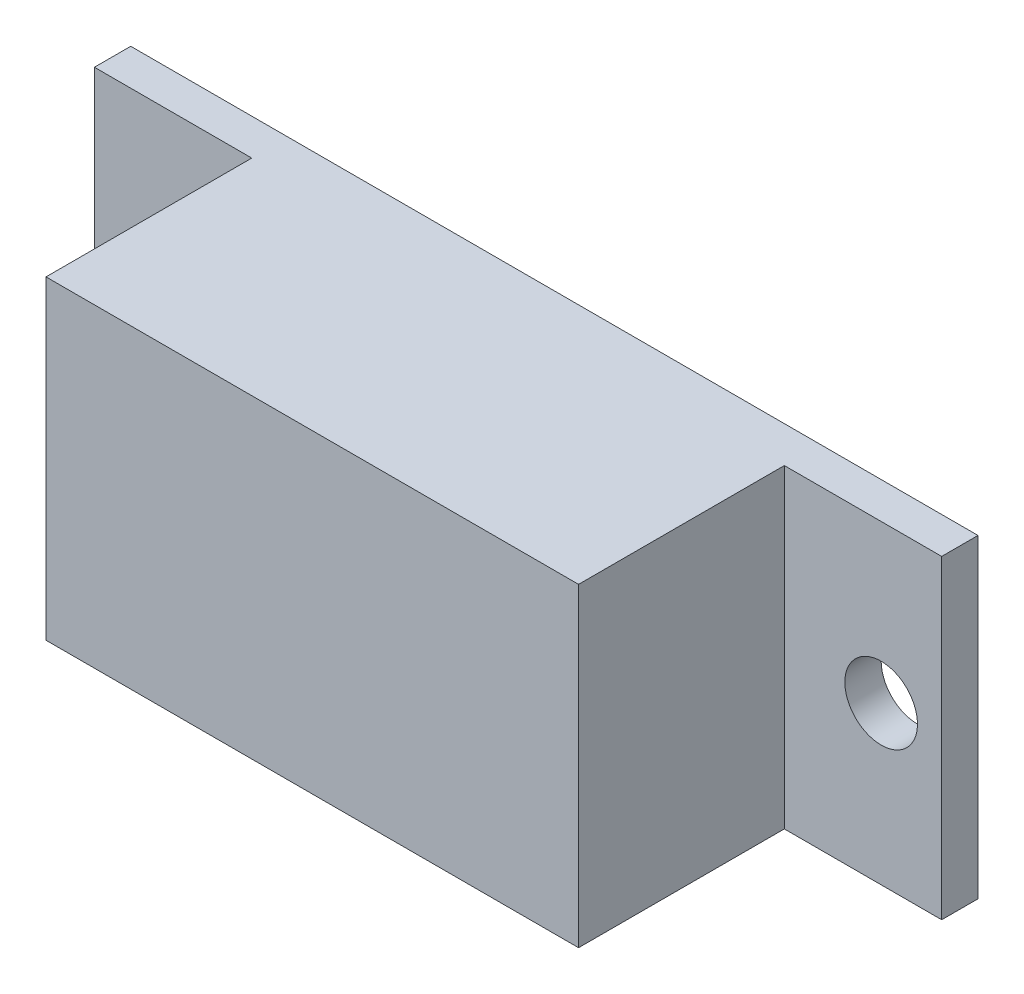
SolidWorks part; units mm, degrees
ref_plane "Plano frontal" through (0, 0, 0) normal (0, 0, 1) x (1, 0, 0)
ref_plane "Plano superior" through (0, 0, 0) normal (0, 1, 0) x (1, 0, 0)
ref_plane "Plano direito" through (0, 0, 0) normal (1, 0, 0) x (0, 0, -1)
sketch "Esboço1" plane through (0, 0, 0) normal (0, 0, 1) x (1, 0, 0)
  line L1 (0, 0) -> (35, 0)
  line L2 (0, 0) -> (0, 13)
  line L3 (0, 13) -> (35, 13)
  line L4 (35, 0) -> (35, 13)
  dimension "D1" = 35
  dimension "D2" = 13
extrude "Ressalto-extrusão1" add sketch "Esboço1" along normal blind 1.5
sketch "Esboço2" plane through (0, 0, 1.5) normal (0, 0, 1) x (1, 0, 0)
  line L0 (0, 13) -> (0, 0) construction
  line L1 (6.5, 13) -> (28.5, 13)
  line L2 (6.5, 13) -> (6.5, 0)
  line L3 (6.5, 0) -> (28.5, 0)
  line L4 (28.5, 13) -> (28.5, 0)
  line L5 (0, 0) -> (35, 0) construction
  dimension "D1" = 22
  dimension "D2" = 6.5
  dimension "D3" = 13
  dimension "D4" = 0
extrude "Ressalto-extrusão2" add sketch "Esboço2" along normal blind 8.5
sketch "Esboço3" plane through (0, 0, 0) normal (0, 0, -1) x (-1, 0, 0)
  line L0 (-35, 13) -> (0, 13) construction
  line L1 (-27.5, 11.25) -> (-7.5, 11.25)
  line L2 (-27.5, 11.25) -> (-27.5, 1.4797)
  line L3 (-27.5, 1.4797) -> (-7.5, 1.4797)
  line L4 (-7.5, 11.25) -> (-7.5, 1.4797)
  line L5 (-35, 0) -> (-35, 13) construction
  dimension "D1" = 20
  dimension "D2" = 1.75
  dimension "D3" = 7.5
extrude "Corte-extrusão1" cut sketch "Esboço3" against normal blind 2.5
sketch "Esboço4" plane through (0, 0, 0) normal (0, 0, -1) x (-1, 0, 0)
  line L0 (-35, 0) -> (-35, 13) construction
  line L1 (0, 13) -> (0, 0) construction
  circle A0 centre (-32.5, 6.5) radius 1.5
  circle A1 centre (-2.5, 6.5) radius 1.5
  point P6 (0, 0)
  dimension "D1" = 3
  dimension "D2" = 3
  dimension "D3" = 2.5
  dimension "D4" = 2.5
extrude "Corte-extrusão2" cut sketch "Esboço4" against normal blind 2.5
